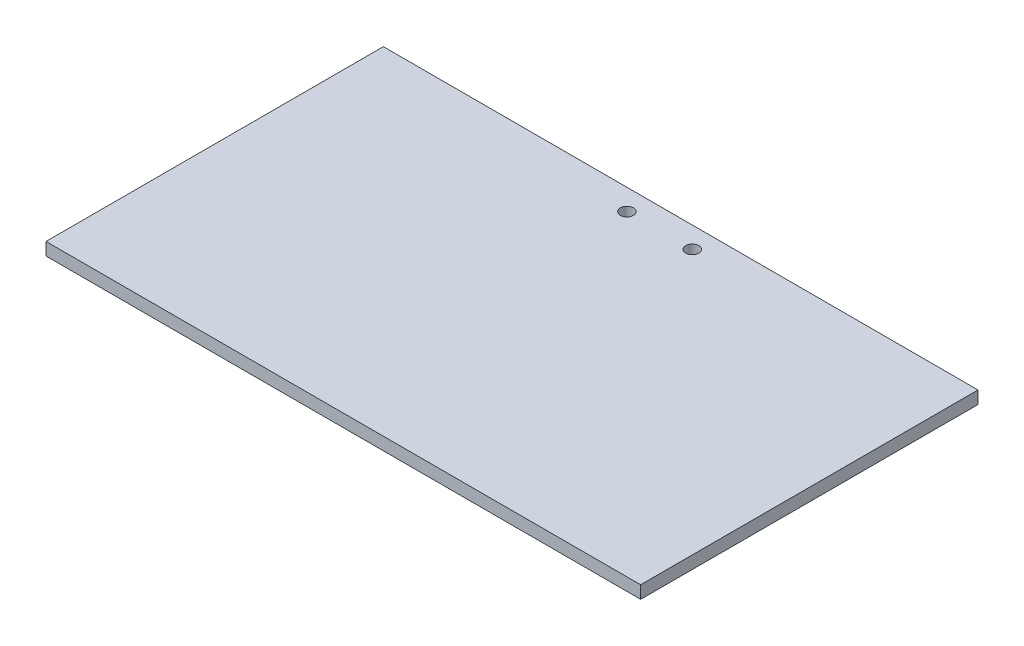
SolidWorks part; units mm, degrees
material "ｱｸﾘﾙ (中-上級の耐衝撃性)"
ref_plane "正面" through (0, 0, 0) normal (0, 0, 1) x (1, 0, 0)
ref_plane "平面" through (0, 0, 0) normal (0, 1, 0) x (1, 0, 0)
ref_plane "右側面" through (0, 0, 0) normal (1, 0, 0) x (0, 0, -1)
sketch "ｽｹｯﾁ1" plane through (0, 0, 0) normal (0, 1, 0) x (1, 0, 0)
  line L1 (-70.5, 40) -> (70.5, 40)
  line L2 (-70.5, 40) -> (-70.5, -40)
  line L3 (-70.5, -40) -> (70.5, -40)
  line L4 (70.5, 40) -> (70.5, -40)
  line L5 (-70.5, 40) -> (70.5, -40) construction
  line L6 (-70.5, -40) -> (70.5, 40) construction
  point P0 (0, 0)
  dimension "D1" = 80
  dimension "D2" = 141
extrude "ﾎﾞｽ - 押し出し1" add sketch "ｽｹｯﾁ1" along normal blind 3
sketch "ｽｹｯﾁ2" plane through (0, 3, 0) normal (0, 1, 0) x (1, 0, 0)
  line L0 (0, 40) -> (0, 35)
  line L1 (70.5, 40) -> (-70.5, 40) construction
  line L2 (0, 35) -> (7.75, 35)
  line L3 (0, 35) -> (-7.75, 35)
  circle A0 centre (-7.75, 35) radius 1.55
  circle A1 centre (7.75, 35) radius 1.55
  dimension "D4" = 3.1
  dimension "D5" = 3.1
  dimension "D1" = 5
  dimension "D2" = 7.75
  dimension "D3" = 7.75
extrude "ｶｯﾄ - 押し出し1" cut sketch "ｽｹｯﾁ2" against normal blind 3 contours A0 | A1
